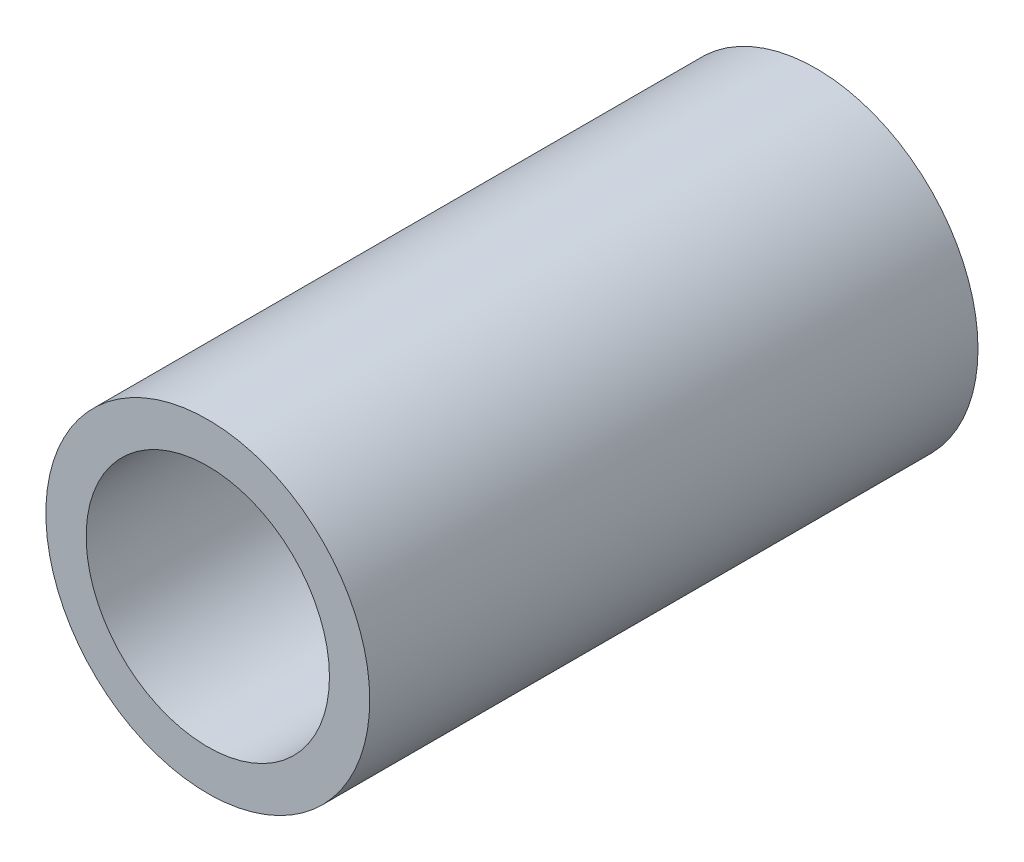
SolidWorks part; units mm, degrees
ref_plane "Ebene vorne" through (0, 0, 0) normal (0, 0, 1) x (1, 0, 0)
ref_plane "Ebene oben" through (0, 0, 0) normal (0, 1, 0) x (1, 0, 0)
ref_plane "Ebene rechts" through (0, 0, 0) normal (1, 0, 0) x (0, 0, -1)
sketch "Skizze1" plane through (0, 0, 0) normal (0, 0, 1) x (1, 0, 0)
  circle A0 centre (0, 0) radius 8
  circle A1 centre (0, 0) radius 10.65
  dimension "D1" = 21.3
  dimension "D2" = 16
extrude "Aufsatz-Linear austragen1" add sketch "Skizze1" along normal blind 40
cosmetic thread "Gewindedarstellung2" parameters "D1"=10, "D2"=18.4887
cosmetic thread "Gewindedarstellung3" parameters "D1"=10, "D2"=18.4887
